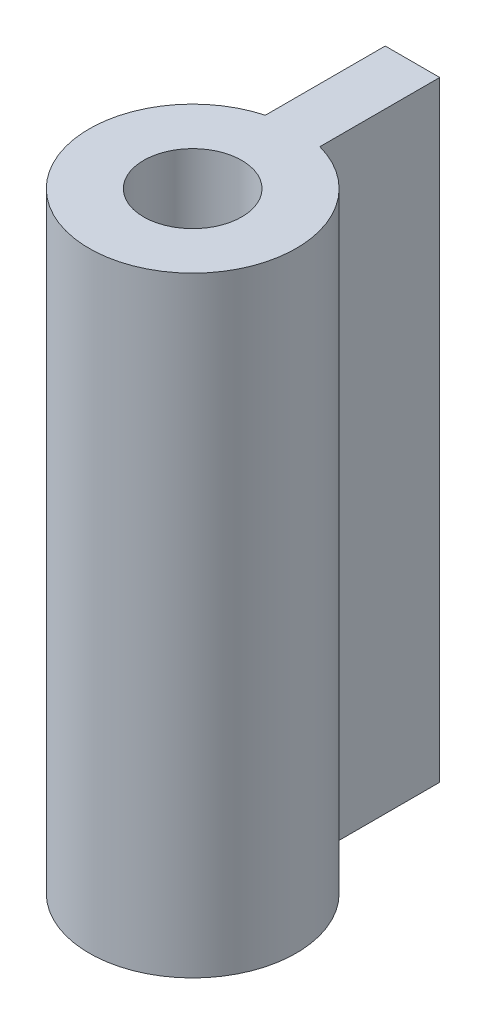
SolidWorks part; units mm, degrees
ref_plane "Front Plane" through (0, 0, 0) normal (0, 0, 1) x (1, 0, 0)
ref_plane "Top Plane" through (0, 0, 0) normal (0, 1, 0) x (1, 0, 0)
ref_plane "Right Plane" through (0, 0, 0) normal (1, 0, 0) x (0, 0, -1)
sketch "Sketch1" plane through (0, 0, 0) normal (0, 1, 0) x (1, 0, 0)
  line L0 (0, 14.1503) -> (0, -21.4931) construction
  line L2 (-1.25, 10.0826) -> (1.25, 10.0826)
  line L3 (-1.25, 10.0826) -> (-1.25, 4.5826)
  line L4 (-1.25, 4.5826) -> (1.25, 4.5826)
  line L5 (1.25, 10.0826) -> (1.25, 4.5826)
  line L6 (-1.25, 10.0826) -> (1.25, 4.5826) construction
  line L7 (-1.25, 4.5826) -> (1.25, 10.0826) construction
  circle A0 centre (0, 0) radius 4.75
  circle A1 centre (0, 0) radius 2.25
  point P5 (0, 7.3326)
  dimension "D1" = 9.5
  dimension "D2" = 4.5
  dimension "D3" = 2.5
  dimension "D4" = 5.5
extrude "Boss-Extrude1" add sketch "Sketch1" along normal blind 28 contours A0 L5 L2 L3 | L4 A0 A1 | L4 A0
